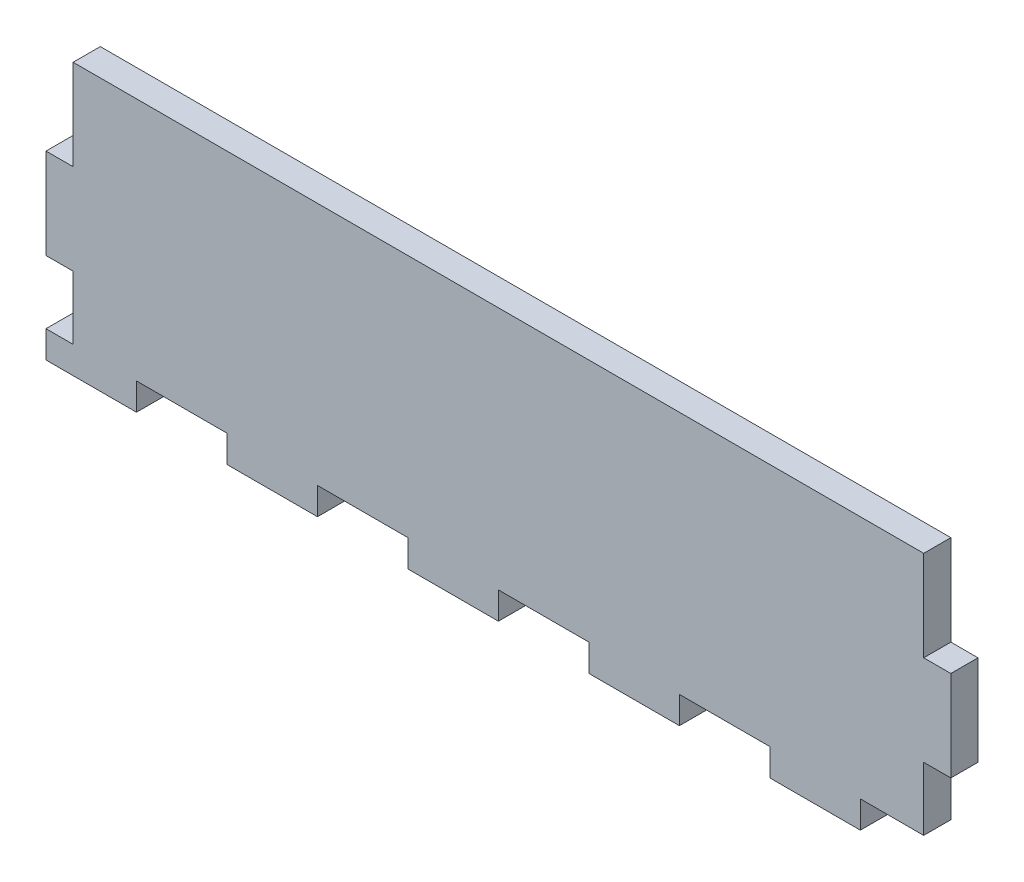
SolidWorks part; units mm, degrees
ref_plane "Front Plane" through (0, 0, 0) normal (0, 0, 1) x (1, 0, 0)
ref_plane "Top Plane" through (0, 0, 0) normal (0, 1, 0) x (1, 0, 0)
ref_plane "Right Plane" through (0, 0, 0) normal (1, 0, 0) x (0, 0, -1)
sketch "Sketch1" plane through (0, 0, 0) normal (0, 0, 1) x (1, 0, 0)
  line L1 (-220.2312, 146.0983) -> (-20.2312, 146.0983)
  line L2 (-220.2312, 146.0983) -> (-220.2312, 86.0983)
  line L3 (-220.2312, 86.0983) -> (-20.2312, 86.0983)
  line L4 (-20.2312, 146.0983) -> (-20.2312, 86.0983)
  dimension "D1" = 60
  dimension "D2" = 200
extrude "Boss-Extrude1" add sketch "Sketch1" along normal blind 6
sketch "Sketch2" plane through (0, 0, 0) normal (0, 0, -1) x (-1, 0, 0)
  line L1 (20.2312, 86.0983) -> (40.2312, 86.0983)
  line L2 (20.2312, 86.0983) -> (20.2312, 92.0983)
  line L3 (20.2312, 92.0983) -> (40.2312, 92.0983)
  line L4 (40.2312, 86.0983) -> (40.2312, 92.0983)
  dimension "D1" = 6
  dimension "D2" = 20
extrude "Cut-Extrude1" cut sketch "Sketch2" against normal blind 10
pattern_linear "LPattern1" count 5 spacing 40 along (-1, 0, 0) of "Cut-Extrude1"
sketch "Sketch3" plane through (0, 0, 0) normal (0, 0, -1) x (-1, 0, 0)
  line L6 (220.2312, 146.0983) -> (220.2312, 86.0983) construction
  line L7 (214.2312, 126.0983) -> (220.2312, 126.0983)
  line L8 (214.2312, 126.0983) -> (214.2312, 146.0983)
  line L9 (214.2312, 146.0983) -> (220.2312, 146.0983)
  line L10 (220.2312, 126.0983) -> (220.2312, 146.0983)
  line L11 (220.2312, 86.0983) -> (200.2312, 86.0983) construction
  dimension "D1" = 20
  dimension "D2" = 40
  dimension "D3" = 6
extrude "Cut-Extrude2" cut sketch "Sketch3" against normal blind 10
sketch "Sketch4" plane through (0, 0, 0) normal (0, 0, -1) x (-1, 0, 0)
  line L0 (20.2312, 92.0983) -> (20.2312, 146.0983) construction
  line L5 (20.2312, 146.0983) -> (26.2312, 146.0983)
  line L6 (20.2312, 146.0983) -> (20.2312, 126.0983)
  line L7 (20.2312, 126.0983) -> (26.2312, 126.0983)
  line L8 (26.2312, 146.0983) -> (26.2312, 126.0983)
  line L9 (20.2312, 146.0983) -> (214.2312, 146.0983) construction
  dimension "D1" = 20
  dimension "0" = 0
  dimension "D3" = 6
extrude "Cut-Extrude3" cut sketch "Sketch4" against normal blind 10
sketch "Sketch6" plane through (0, 0, 0) normal (0, 0, -1) x (-1, 0, 0)
  line L7 (220.2312, 126.0983) -> (220.2312, 86.0983) construction
  line L8 (214.2312, 106.0983) -> (220.2312, 106.0983)
  line L9 (214.2312, 106.0983) -> (214.2312, 92.0983)
  line L10 (214.2312, 92.0983) -> (220.2312, 92.0983)
  line L11 (220.2312, 106.0983) -> (220.2312, 92.0983)
  line L12 (214.2312, 126.0983) -> (220.2312, 126.0983) construction
  line L13 (200.2312, 92.0983) -> (180.2312, 92.0983) construction
  dimension "D1" = 6
  dimension "D2" = 0
  dimension "D3" = 20
extrude "Cut-Extrude4" cut sketch "Sketch6" against normal blind 10
sketch "Sketch7" plane through (0, 0, 0) normal (0, 0, -1) x (-1, 0, 0)
  line L0 (20.2312, 92.0983) -> (20.2312, 126.0983) construction
  line L1 (20.2312, 106.0983) -> (26.2312, 106.0983)
  line L2 (20.2312, 106.0983) -> (20.2312, 92.0983)
  line L3 (20.2312, 92.0983) -> (26.2312, 92.0983)
  line L4 (26.2312, 106.0983) -> (26.2312, 92.0983)
  line L5 (40.2312, 92.0983) -> (20.2312, 92.0983) construction
  line L6 (20.2312, 126.0983) -> (26.2312, 126.0983) construction
  point P10 (23.2312, 126.0983)
  dimension "D1" = 6
  dimension "D2" = 20
extrude "Cut-Extrude5" cut sketch "Sketch7" against normal blind 10
